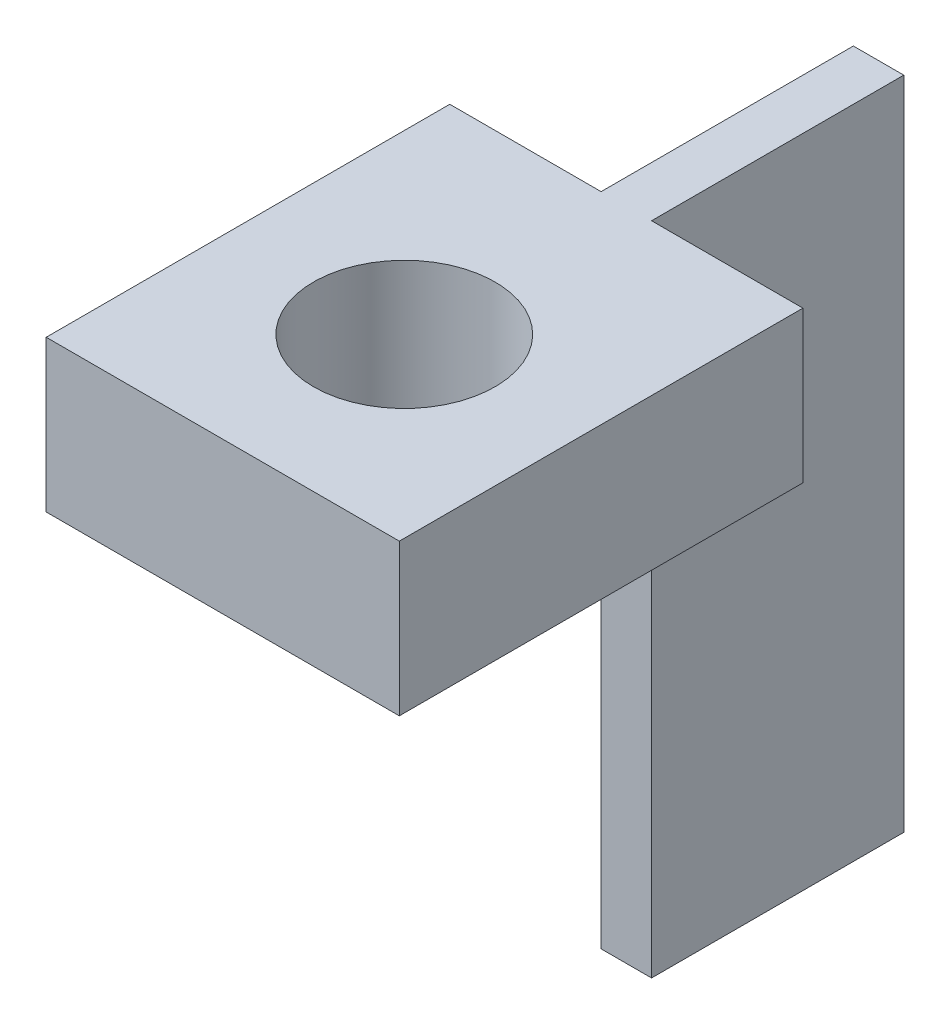
SolidWorks part; units mm, degrees
ref_plane "Front Plane" through (0, 0, 0) normal (0, 0, 1) x (1, 0, 0)
ref_plane "Top Plane" through (0, 0, 0) normal (0, 1, 0) x (1, 0, 0)
ref_plane "Right Plane" through (0, 0, 0) normal (1, 0, 0) x (0, 0, -1)
sketch "Sketch1" plane through (0, 0, 0) normal (1, 0, 0) x (0, 0, -1)
  line L0 (0, 0) -> (0, 10)
  line L1 (0, 10) -> (-8, 10)
  line L2 (-8, 10) -> (-8, 13)
  line L3 (-8, 13) -> (5, 13)
  line L4 (5, 13) -> (5, 0)
  line L5 (5, 0) -> (0, 0)
  dimension "D1" = 10
  dimension "D2" = 5
  dimension "D3" = 8
  dimension "D4" = 3
extrude "Boss-Extrude1" add sketch "Sketch1" along normal mid plane 1
sketch "Sketch2" plane through (0, 10, 0) normal (0, -1, 0) x (1, 0, 0)
  line L0 (0.5, 8) -> (-0.5, 8) construction
  line L1 (-3.5, 8) -> (3.5, 8)
  line L2 (-3.5, 8) -> (-3.5, 0)
  line L3 (-3.5, 0) -> (3.5, 0)
  line L4 (3.5, 8) -> (3.5, 0)
  line L5 (0, 0) -> (0, 8) construction
  line L6 (-3.5, 4) -> (3.5, 4) construction
  point P4 (0, 0)
  point P5 (0, 8)
  point P164 (0, 4)
  dimension "D1" = 7
extrude "Boss-Extrude2" add sketch "Sketch2" against normal through all
hole_wizard "M3 Clearance Hole1" positions "Sketch3" profile "Sketch4" hole size "M3" standard "ANSI Metric" end condition through all
sketch "Sketch3" plane through (0, 13, 0) normal (0, 1, 0) x (1, 0, 0)
  point P0 (0, -4.4016)
sketch "Sketch4" plane through (0, 13, 4.4016) normal (1, 0, 0) x (0, 0, 1)
  line L0 (0, 0) -> (0, 13)
  line L1 (0, 13) -> (1.8, 13)
  line L2 (1.8, 13) -> (1.8, 0)
  line L5 (1.8, 0) -> (0, 0)
  line L11 (0, -6.35) -> (0, 107.95) construction
  dimension "Thru Hole Dia." = 3.6
  dimension "Thru Hole Depth" = 13
